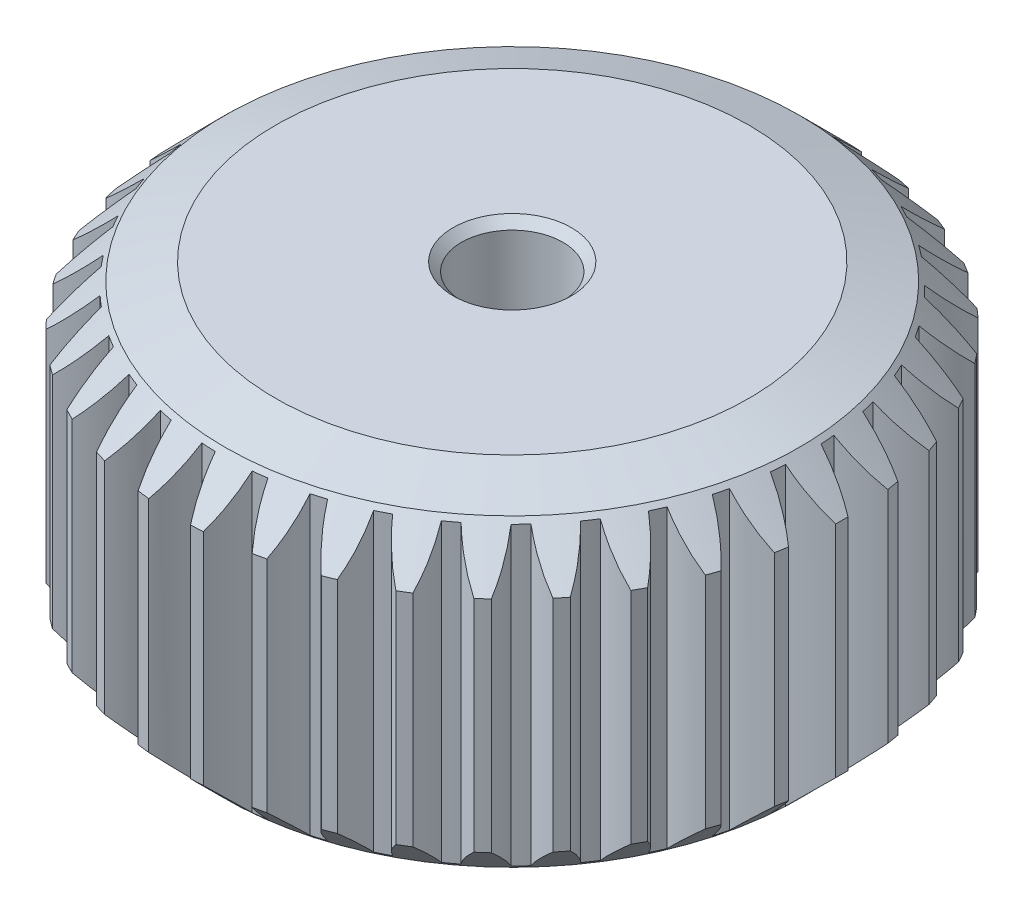
SolidWorks part; units mm, degrees
ref_plane "前视基准面" through (0, 0, 0) normal (0, 0, 1) x (1, 0, 0)
ref_plane "上视基准面" through (0, 0, 0) normal (0, 1, 0) x (1, 0, 0)
ref_plane "右视基准面" through (0, 0, 0) normal (1, 0, 0) x (0, 0, -1)
sketch "草图1" plane through (0, 0, 0) normal (0, 1, 0) x (1, 0, 0)
  line L0 (0, 0) -> (0, 23.6314) construction
  line L1 (0, 0) -> (6.6694, 18.324) construction
  line L2 (0, 0) -> (1.1876, 27.9573) construction
  line L3 (0, 18.5) -> (5.9458, 16.3359) construction
  circle A0 centre (0, 0) radius 19.5 construction
  circle A1 centre (0, 0) radius 17.25 construction
  circle A2 centre (0, 0) radius 18.5 construction
  circle A3 centre (5.9458, 16.3359) radius 6.3274 construction
  arc A4 (0.4632, 19.4945) -> (-0.3156, 17.2471) centre (5.9458, 16.3359) ccw
  arc A5 (1.1917, 19.4635) -> (1.7772, 17.1582) centre (-4.539, 16.7813) cw
  arc A6 (0.4632, 19.4945) -> (1.1917, 19.4635) centre (0, 0) cw
  arc A7 (-0.3156, 17.2471) -> (1.7772, 17.1582) centre (0, 0) cw
  arc A8 (2.6037, 17.0524) -> (4.6513, 16.6111) centre (0, 0) cw
  arc A9 (4.464, 18.9822) -> (4.6513, 16.6111) centre (-1.6376, 17.307) cw
  arc A10 (3.7511, 19.1358) -> (4.464, 18.9822) centre (0, 0) cw
  arc A11 (3.7511, 19.1358) -> (2.6037, 17.0524) centre (8.621, 15.0961) ccw
  arc A12 (5.4481, 16.3671) -> (7.3917, 15.5861) centre (0, 0) cw
  arc A13 (7.6077, 17.9547) -> (7.3917, 15.5861) centre (1.3108, 17.3348) cw
  arc A14 (6.9311, 18.2266) -> (7.6077, 17.9547) centre (0, 0) cw
  arc A15 (6.9311, 18.2266) -> (5.4481, 16.3671) centre (11.0483, 13.422) ccw
  arc A16 (8.1358, 15.2109) -> (9.9195, 14.1127) centre (0, 0) cw
  arc A17 (10.5327, 16.4107) -> (9.9195, 14.1127) centre (4.2216, 16.8639) cw
  arc A18 (9.9117, 16.7931) -> (10.5327, 16.4107) centre (0, 0) cw
  arc A19 (9.9117, 16.7931) -> (8.1358, 15.2109) centre (13.1577, 11.3618) ccw
  arc A20 (10.5894, 13.6172) -> (12.1618, 12.2333) centre (0, 0) cw
  arc A21 (13.1546, 14.3947) -> (12.1618, 12.2333) centre (7.0109, 15.9079) cw
  arc A22 (12.6072, 14.8764) -> (13.1546, 14.3947) centre (0, 0) cw
  arc A23 (12.6072, 14.8764) -> (10.5894, 13.6172) centre (14.8886, 8.9747) ccw
  arc A24 (12.7384, 11.6317) -> (14.0543, 10.0019) centre (0, 0) cw
  arc A25 (15.3981, 11.9645) -> (14.0543, 10.0019) centre (9.5985, 14.4943) cw
  arc A26 (14.94, 12.5318) -> (15.3981, 11.9645) centre (0, 0) cw
  arc A27 (14.94, 12.5318) -> (12.7384, 11.6317) centre (16.1911, 6.3294) ccw
  arc A28 (14.5209, 9.3116) -> (15.5425, 7.4829) centre (0, 0) cw
  arc A29 (17.1986, 9.1901) -> (15.5425, 7.4829) centre (11.9099, 12.6636) cw
  arc A30 (16.843, 9.8267) -> (17.1986, 9.1901) centre (0, 0) cw
  arc A31 (16.843, 9.8267) -> (14.5209, 9.3116) centre (17.0279, 3.502) ccw
  arc A32 (15.8857, 6.7236) -> (16.5835, 4.7485) centre (0, 0) cw
  arc A33 (18.5044, 6.1513) -> (16.5835, 4.7485) centre (13.8788, 10.4687) cw
  arc A34 (18.2614, 6.8389) -> (18.5044, 6.1513) centre (0, 0) cw
  arc A35 (18.2614, 6.8389) -> (15.8857, 6.7236) centre (17.3748, 0.5739) ccw
  arc A36 (16.7935, 3.9422) -> (17.1475, 1.8776) centre (0, 0) cw
  arc A37 (19.2778, 2.9356) -> (17.1475, 1.8776) centre (15.4484, 7.9726) cw
  arc A38 (19.1545, 3.6543) -> (19.2778, 2.9356) centre (0, 0) cw
  arc A39 (19.1545, 3.6543) -> (16.7935, 3.9422) centre (17.2219, -2.3707) ccw
  arc A40 (17.2182, 1.0473) -> (17.2182, -1.0473) centre (0, 0) cw
  arc A41 (19.4966, -0.3646) -> (17.2182, -1.0473) centre (16.5735, 5.2471) cw
  arc A42 (19.4966, 0.3646) -> (19.4966, -0.3646) centre (0, 0) cw
  arc A43 (19.4966, 0.3646) -> (17.2182, 1.0473) centre (16.5735, -5.2471) ccw
  arc A44 (17.1475, -1.8776) -> (16.7935, -3.9422) centre (0, 0) cw
  arc A45 (19.1545, -3.6543) -> (16.7935, -3.9422) centre (17.2219, 2.3707) cw
  arc A46 (19.2778, -2.9356) -> (19.1545, -3.6543) centre (0, 0) cw
  arc A47 (19.2778, -2.9356) -> (17.1475, -1.8776) centre (15.4484, -7.9726) ccw
  arc A48 (16.5835, -4.7485) -> (15.8857, -6.7236) centre (0, 0) cw
  arc A49 (18.2614, -6.8389) -> (15.8857, -6.7236) centre (17.3748, -0.5739) cw
  arc A50 (18.5044, -6.1513) -> (18.2614, -6.8389) centre (0, 0) cw
  arc A51 (18.5044, -6.1513) -> (16.5835, -4.7485) centre (13.8788, -10.4687) ccw
  arc A52 (15.5425, -7.4829) -> (14.5209, -9.3116) centre (0, 0) cw
  arc A53 (16.843, -9.8267) -> (14.5209, -9.3116) centre (17.0279, -3.502) cw
  arc A54 (17.1986, -9.1901) -> (16.843, -9.8267) centre (0, 0) cw
  arc A55 (17.1986, -9.1901) -> (15.5425, -7.4829) centre (11.9099, -12.6636) ccw
  arc A56 (14.0543, -10.0019) -> (12.7384, -11.6317) centre (0, 0) cw
  arc A57 (14.94, -12.5318) -> (12.7384, -11.6317) centre (16.1911, -6.3294) cw
  arc A58 (15.3981, -11.9645) -> (14.94, -12.5318) centre (0, 0) cw
  arc A59 (15.3981, -11.9645) -> (14.0543, -10.0019) centre (9.5985, -14.4943) ccw
  arc A60 (12.1618, -12.2333) -> (10.5894, -13.6172) centre (0, 0) cw
  arc A61 (12.6072, -14.8764) -> (10.5894, -13.6172) centre (14.8886, -8.9747) cw
  arc A62 (13.1546, -14.3947) -> (12.6072, -14.8764) centre (0, 0) cw
  arc A63 (13.1546, -14.3947) -> (12.1618, -12.2333) centre (7.0109, -15.9079) ccw
  arc A64 (9.9195, -14.1127) -> (8.1358, -15.2109) centre (0, 0) cw
  arc A65 (9.9117, -16.7931) -> (8.1358, -15.2109) centre (13.1577, -11.3618) cw
  arc A66 (10.5327, -16.4107) -> (9.9117, -16.7931) centre (0, 0) cw
  arc A67 (10.5327, -16.4107) -> (9.9195, -14.1127) centre (4.2216, -16.8639) ccw
  arc A68 (7.3917, -15.5861) -> (5.4481, -16.3671) centre (0, 0) cw
  arc A69 (6.9311, -18.2266) -> (5.4481, -16.3671) centre (11.0483, -13.422) cw
  arc A70 (7.6077, -17.9547) -> (6.9311, -18.2266) centre (0, 0) cw
  arc A71 (7.6077, -17.9547) -> (7.3917, -15.5861) centre (1.3108, -17.3348) ccw
  arc A72 (4.6513, -16.6111) -> (2.6037, -17.0524) centre (0, 0) cw
  arc A73 (3.7511, -19.1358) -> (2.6037, -17.0524) centre (8.621, -15.0961) cw
  arc A74 (4.464, -18.9822) -> (3.7511, -19.1358) centre (0, 0) cw
  arc A75 (4.464, -18.9822) -> (4.6513, -16.6111) centre (-1.6376, -17.307) ccw
  arc A76 (1.7772, -17.1582) -> (-0.3156, -17.2471) centre (0, 0) cw
  arc A77 (0.4632, -19.4945) -> (-0.3156, -17.2471) centre (5.9458, -16.3359) cw
  arc A78 (1.1917, -19.4635) -> (0.4632, -19.4945) centre (0, 0) cw
  arc A79 (1.1917, -19.4635) -> (1.7772, -17.1582) centre (-4.539, -16.7813) ccw
  arc A80 (-1.1482, -17.2117) -> (-3.2259, -16.9457) centre (0, 0) cw
  arc A81 (-2.8381, -19.2924) -> (-3.2259, -16.9457) centre (3.0995, -17.1058) cw
  arc A82 (-2.1148, -19.385) -> (-2.8381, -19.2924) centre (0, 0) cw
  arc A83 (-2.1148, -19.385) -> (-1.1482, -17.2117) centre (-7.3097, -15.7728) ccw
  arc A84 (-4.0404, -16.7701) -> (-6.0433, -16.1568) centre (0, 0) cw
  arc A85 (-6.0577, -18.5352) -> (-6.0433, -16.1568) centre (0.164, -17.3835) cw
  arc A86 (-5.3604, -18.7488) -> (-6.0577, -18.5352) centre (0, 0) cw
  arc A87 (-5.3604, -18.7488) -> (-4.0404, -16.7701) centre (-9.8702, -14.3106) ccw
  arc A88 (-6.8165, -15.8461) -> (-8.6869, -14.903) centre (0, 0) cw
  arc A89 (-9.103, -17.2449) -> (-8.6869, -14.903) centre (-2.7762, -17.1612) cw
  arc A90 (-8.4519, -17.5732) -> (-9.103, -17.2449) centre (0, 0) cw
  arc A91 (-8.4519, -17.5732) -> (-6.8165, -15.8461) centre (-12.1468, -12.4367) ccw
  arc A92 (-9.3964, -14.4661) -> (-11.0806, -13.2206) centre (0, 0) cw
  arc A93 (-11.8865, -15.4584) -> (-11.0806, -13.2206) centre (-5.6365, -16.4452) cw
  arc A94 (-11.3002, -15.892) -> (-11.8865, -15.4584) centre (0, 0) cw
  arc A95 (-11.3002, -15.892) -> (-9.3964, -14.4661) centre (-14.0738, -10.205) ccw
  arc A96 (-11.7061, -12.6701) -> (-13.1555, -11.1578) centre (0, 0) cw
  arc A97 (-14.328, -13.2272) -> (-13.1555, -11.1578) centre (-8.3347, -15.2561) cw
  arc A98 (-13.8234, -13.7537) -> (-14.328, -13.2272) centre (0, 0) cw
  arc A99 (-13.8234, -13.7537) -> (-11.7061, -12.6701) centre (-15.596, -7.6797) ccw
  arc A100 (-13.6789, -10.5095) -> (-14.8519, -8.774) centre (0, 0) cw
  arc A101 (-16.3573, -10.6155) -> (-14.8519, -8.774) centre (-10.7931, -13.628) cw
  arc A102 (-15.9489, -11.2197) -> (-16.3573, -10.6155) centre (0, 0) cw
  arc A103 (-15.9489, -11.2197) -> (-13.6789, -10.5095) centre (-16.6696, -4.9335) ccw
  arc A104 (-15.2583, -8.0466) -> (-16.1211, -6.1378) centre (0, 0) cw
  arc A105 (-17.916, -7.6984) -> (-16.1211, -6.1378) centre (-12.941, -11.608) cw
  arc A106 (-17.6157, -8.3629) -> (-17.916, -7.6984) centre (0, 0) cw
  arc A107 (-17.6157, -8.3629) -> (-15.2583, -8.0466) centre (-17.2636, -2.0453) ccw
  arc A108 (-16.3987, -5.3521) -> (-16.9265, -3.3251) centre (0, 0) cw
  arc A109 (-18.9594, -4.5599) -> (-16.9265, -3.3251) centre (-14.7166, -9.254) cw
  arc A110 (-18.7756, -5.2656) -> (-18.9594, -4.5599) centre (0, 0) cw
  arc A111 (-18.7756, -5.2656) -> (-16.3987, -5.3521) centre (-17.3609, 0.9016) ccw
  arc A112 (-17.0673, -2.5038) -> (-17.245, -0.4166) centre (0, 0) cw
  arc A113 (-19.4573, -1.2901) -> (-17.245, -0.4166) centre (-16.0688, -6.6337) cw
  arc A114 (-19.3954, -2.0167) -> (-19.4573, -1.2901) centre (0, 0) cw
  arc A115 (-19.3954, -2.0167) -> (-17.0673, -2.5038) centre (-16.9588, 3.8227) ccw
  arc A116 (-17.245, 0.4166) -> (-17.0673, 2.5038) centre (0, 0) cw
  arc A117 (-19.3954, 2.0167) -> (-17.0673, 2.5038) centre (-16.9588, -3.8227) cw
  arc A118 (-19.4573, 1.2901) -> (-19.3954, 2.0167) centre (0, 0) cw
  arc A119 (-19.4573, 1.2901) -> (-17.245, 0.4166) centre (-16.0688, 6.6337) ccw
  arc A120 (-16.9265, 3.3251) -> (-16.3987, 5.3521) centre (0, 0) cw
  arc A121 (-18.7756, 5.2656) -> (-16.3987, 5.3521) centre (-17.3609, -0.9016) cw
  arc A122 (-18.9594, 4.5599) -> (-18.7756, 5.2656) centre (0, 0) cw
  arc A123 (-18.9594, 4.5599) -> (-16.9265, 3.3251) centre (-14.7166, 9.254) ccw
  arc A124 (-16.1211, 6.1378) -> (-15.2583, 8.0466) centre (0, 0) cw
  arc A125 (-17.6157, 8.3629) -> (-15.2583, 8.0466) centre (-17.2636, 2.0453) cw
  arc A126 (-17.916, 7.6984) -> (-17.6157, 8.3629) centre (0, 0) cw
  arc A127 (-17.916, 7.6984) -> (-16.1211, 6.1378) centre (-12.941, 11.608) ccw
  arc A128 (-14.8519, 8.774) -> (-13.6789, 10.5095) centre (0, 0) cw
  arc A129 (-15.9489, 11.2197) -> (-13.6789, 10.5095) centre (-16.6696, 4.9335) cw
  arc A130 (-16.3573, 10.6155) -> (-15.9489, 11.2197) centre (0, 0) cw
  arc A131 (-16.3573, 10.6155) -> (-14.8519, 8.774) centre (-10.7931, 13.628) ccw
  arc A132 (-13.1555, 11.1578) -> (-11.7061, 12.6701) centre (0, 0) cw
  arc A133 (-13.8234, 13.7537) -> (-11.7061, 12.6701) centre (-15.596, 7.6797) cw
  arc A134 (-14.328, 13.2272) -> (-13.8234, 13.7537) centre (0, 0) cw
  arc A135 (-14.328, 13.2272) -> (-13.1555, 11.1578) centre (-8.3347, 15.2561) ccw
  arc A136 (-11.0806, 13.2206) -> (-9.3964, 14.4661) centre (0, 0) cw
  arc A137 (-11.3002, 15.892) -> (-9.3964, 14.4661) centre (-14.0738, 10.205) cw
  arc A138 (-11.8865, 15.4584) -> (-11.3002, 15.892) centre (0, 0) cw
  arc A139 (-11.8865, 15.4584) -> (-11.0806, 13.2206) centre (-5.6365, 16.4452) ccw
  arc A140 (-8.6869, 14.903) -> (-6.8165, 15.8461) centre (0, 0) cw
  arc A141 (-8.4519, 17.5732) -> (-6.8165, 15.8461) centre (-12.1468, 12.4367) cw
  arc A142 (-9.103, 17.2449) -> (-8.4519, 17.5732) centre (0, 0) cw
  arc A143 (-9.103, 17.2449) -> (-8.6869, 14.903) centre (-2.7762, 17.1612) ccw
  arc A144 (-6.0433, 16.1568) -> (-4.0404, 16.7701) centre (0, 0) cw
  arc A145 (-5.3604, 18.7488) -> (-4.0404, 16.7701) centre (-9.8702, 14.3106) cw
  arc A146 (-6.0577, 18.5352) -> (-5.3604, 18.7488) centre (0, 0) cw
  arc A147 (-6.0577, 18.5352) -> (-6.0433, 16.1568) centre (0.164, 17.3835) ccw
  arc A148 (-3.2259, 16.9457) -> (-1.1482, 17.2117) centre (0, 0) cw
  arc A149 (-2.1148, 19.385) -> (-1.1482, 17.2117) centre (-7.3097, 15.7728) cw
  arc A150 (-2.8381, 19.2924) -> (-2.1148, 19.385) centre (0, 0) cw
  arc A151 (-2.8381, 19.2924) -> (-3.2259, 16.9457) centre (3.0995, 17.1058) ccw
  point P237 (0, 0)
  dimension "D1" = 34.5
  dimension "D2" = 37
  dimension "D3" = 39
  dimension "D4" = 20
  dimension "D5" = 2.432
  dimension "D6" = 37
extrude "凸台-拉伸1" add sketch "草图1" along normal blind 20
sketch "草图2" plane through (0, 0, 0) normal (0, 1, 0) x (1, 0, 0)
  circle A0 centre (0, 0) radius 17.25
extrude "凸台-拉伸2" add sketch "草图2" along normal blind 20
sketch "草图3" plane through (0, 20, 0) normal (0, 1, 0) x (1, 0, 0)
  circle A0 centre (0, 0) radius 3
  dimension "D1" = 6
extrude "切除-拉伸1" cut sketch "草图3" against normal through all both and the other way through all
sketch "草图4" plane through (0, 0, 0) normal (1, 0, 0) x (0, 0, -1)
  line L0 (0, 0) -> (0, 23.1258) construction
  line L1 (-0.3646, 0) -> (0.3646, 0) construction
  line L2 (14, 20) -> (20, 20)
  line L3 (20, 20) -> (20, 18)
  line L4 (20, 18) -> (14, 20)
  line L5 (20, 2) -> (14, 0)
  line L6 (14, 0) -> (20, 0)
  line L7 (20, 0) -> (20, 2)
  point P9 (20, 18.0522)
  point P11 (20, 1.8595)
  point P12 (20, 18.03)
  dimension "D1" = 6
  dimension "D2" = 20
  dimension "D3" = 20
  dimension "D4" = 2
revolve "切除-旋转1" cut sketch "草图4" angle 360 about L0
sketch "草图5" plane through (0, 0, 0) normal (1, 0, 0) x (0, 0, -1)
  line L0 (0, 0) -> (0, 25.8417) construction
  line L1 (16, 20) -> (19.5, 16.5)
  line L2 (19.5, 16.5) -> (19.5, 20)
  line L3 (19.5, 20) -> (16, 20)
  line L4 (14, 20) -> (-14, 20) construction
  line L5 (0, 10) -> (27.9569, 10) construction
  line L6 (19.5, 3.5) -> (19.5, 0)
  line L7 (16, 0) -> (19.5, 3.5)
  line L8 (19.5, 0) -> (16, 0)
  dimension "D1" = 3.5
  dimension "D2" = 19.5
  dimension "D3" = 10
revolve "切除-旋转2" cut sketch "草图5" angle 360 about L0
chamfer "倒角1" distance 0.5 angle 45 2 edges at (0, 0, 3) (0, 20, -3)
